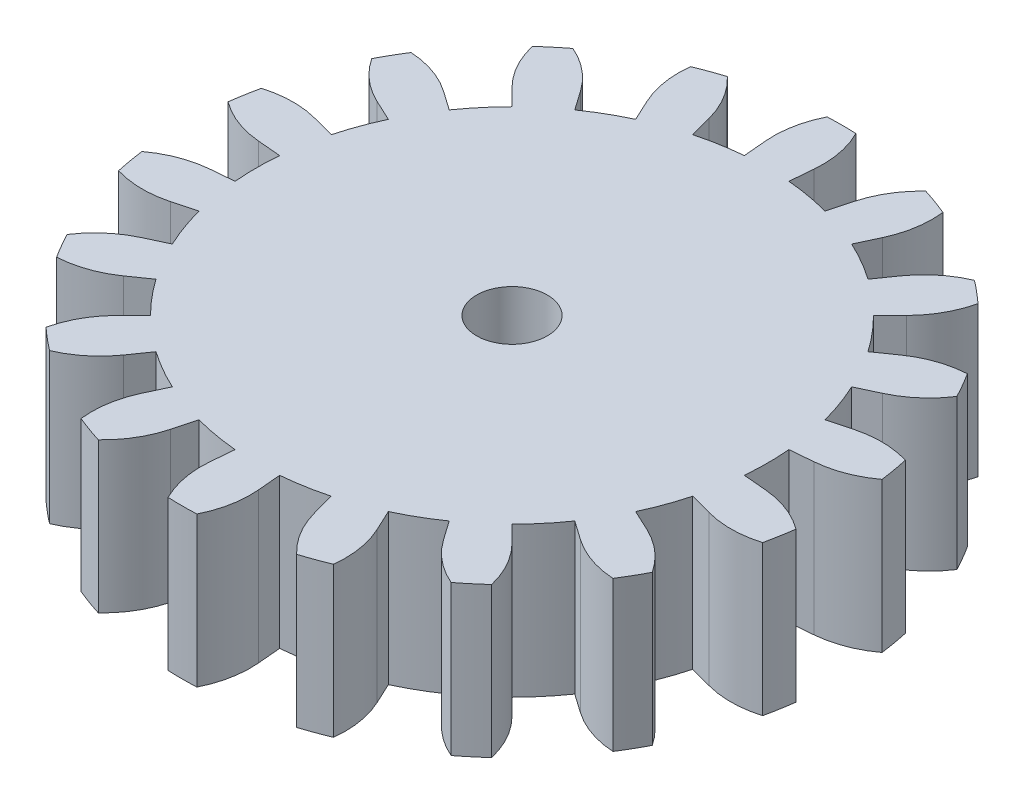
SolidWorks part; units mm, degrees
ref_plane "Front Plane" through (0, 0, 0) normal (0, 0, 1) x (1, 0, 0)
ref_plane "Top Plane" through (0, 0, 0) normal (0, 1, 0) x (1, 0, 0)
ref_plane "Right Plane" through (0, 0, 0) normal (1, 0, 0) x (0, 0, -1)
sketch "Sketch1" plane through (0, 0, 0) normal (0, 1, 0) x (1, 0, 0)
  line L0 (0, 0) -> (0, 13.97) construction
  line L1 (0, 0) -> (-0.6094, 13.9567) construction
  line L2 (0, 0) -> (-1.0297, 11.7695) construction
  line L3 (0, 0) -> (-1.88, 10.6623) construction
  line L4 (0, 0) -> (-1.88, 10.6623)
  line L5 (-0.9436, 10.7856) -> (-1.0297, 11.7695)
  line L6 (0, 0) -> (1.88, 10.6623)
  line L7 (0.9436, 10.7856) -> (1.0297, 11.7695)
  circle A0 centre (0, 0) radius 13.97 construction
  circle A1 centre (0, 0) radius 11.8144 construction
  circle A2 centre (0, 0) radius 10.8268 construction
  arc A3 (-1.88, 10.6623) -> (-0.9436, 10.7856) centre (0, 0) cw
  arc A4 (-1.0297, 11.7695) -> (-0.6094, 13.9567) centre (3.0252, 12.1242) cw
  arc A5 (-0.6094, 13.9567) -> (0.6094, 13.9567) centre (0, 0) cw
  arc A6 (1.88, 10.6623) -> (0.9436, 10.7856) centre (0, 0) ccw
  arc A7 (1.0297, 11.7695) -> (0.6094, 13.9567) centre (-3.0252, 12.1242) ccw
  dimension "D1" = 27.94
  dimension "D2" = 23.6289
  dimension "D3" = 3.1433
  dimension "D4" = 10
  dimension "D5" = 5
  dimension "D6" = 2.5
extrude "Boss-Extrude1" add sketch "Sketch1" along normal blind 6.35
pattern_circular "CirPattern1" count 18 every 20 about axis through (0, 0, 0) along (0, 1, 0) of "Boss-Extrude1"
sketch "Sketch2" plane through (0, 6.35, 0) normal (0, 1, 0) x (1, 0, 0)
  circle A0 centre (0, 0) radius 1.5
  dimension "D1" = 3
extrude "Cut-Extrude1" cut sketch "Sketch2" against normal blind 6.35
